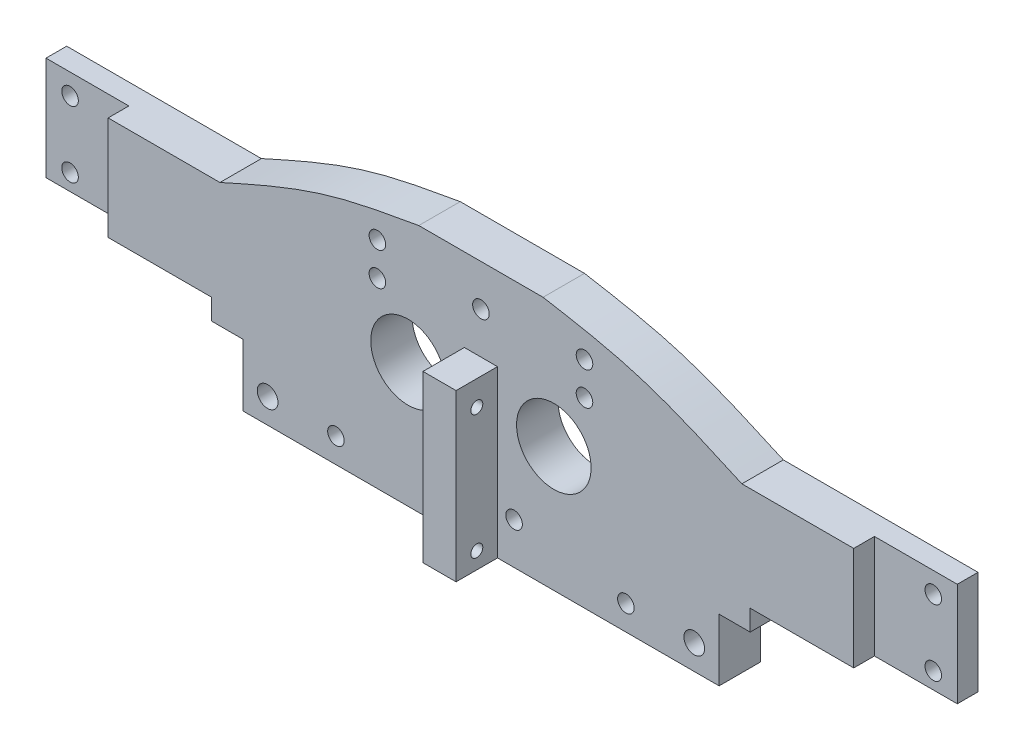
SolidWorks part; units mm, degrees
material "PLA Black"
ref_plane "Front Plane" through (0, 0, 0) normal (0, 0, 1) x (1, 0, 0)
ref_plane "Top Plane" through (0, 0, 0) normal (0, 1, 0) x (1, 0, 0)
ref_plane "Right Plane" through (0, 0, 0) normal (1, 0, 0) x (0, 0, -1)
sketch "Sketch1" plane through (0, 0, 0) normal (0, 0, 1) x (1, 0, 0)
  line L1 (-65, -22.5) -> (65, -22.5)
  line L2 (-65, -22.5) -> (-65, 7.5)
  line L3 (-65, 7.5) -> (-63, 7.5)
  line L4 (65, -22.5) -> (65, 7.5)
  line L5 (-15, 22.5) -> (15, 22.5)
  line L7 (63, 7.5) -> (65, 7.5)
  line L8 (0, 22.5) -> (0, -22.5) construction
  spline S0 degree 3 poles (15, 22.5) (22.4466, 21.1973) (39.0797, 18.2875) (54.4893, 11.3381) (63, 7.5) knots 0 0 0 0 0.4477 1 1 1 1
  spline S1 degree 3 poles (-15, 22.5) (-22.4466, 21.1973) (-39.0797, 18.2875) (-54.4893, 11.3381) (-63, 7.5) knots 0 0 0 0 0.4477 1 1 1 1
  point P10 (0, -22.5)
  point P11 (0, 0)
  dimension "D1" = 130
  dimension "D2" = 30
  dimension "D3" = 2
  dimension "D4" = 45
  dimension "D5" = 30
extrude "Extrude1" add sketch "Sketch1" along normal blind 10
sketch "Sketch2" plane through (0, 0, 0) normal (0, 0, 1) x (1, 0, 0)
  line L0 (-65, -22.5) -> (65, -22.5) construction
  line L1 (-57.5, -22.5) -> (57.5, -22.5)
  line L2 (-57.5, -22.5) -> (-57.5, -37.5)
  line L3 (-57.5, -37.5) -> (57.5, -37.5)
  line L4 (57.5, -22.5) -> (57.5, -37.5)
  point P6 (0, -37.5)
  dimension "D1" = 15
  dimension "D2" = 115
extrude "Extrude2" add sketch "Sketch2" along normal up to surface (10 mm away) up to face at (6, 3.75, 10)
hole_wizard "Ø4.0 (4) Diameter Hole1" positions "3DSketch1" profile "Sketch3" hole size "Ø4.0" standard "Ansi Metric"
sketch3d "3DSketch1"
  line L0 (57.5, -37.5, 10) -> (-57.5, -37.5, 10) construction
  line L5 (-35, -31.5, 10) -> (35, -31.5, 10) construction
  line L11 (0, -37.5, 10) -> (0, 22.5, 10) construction
  line L12 (15, 22.5, 10) -> (-15, 22.5, 10) construction
  point P0 (-35, -31.5, 10)
  point P2 (35, -31.5, 10)
  point P18 (0, -31.5, 10)
  dimension "D1" = 6
  dimension "D2" = 70
sketch "Sketch3" plane through (-35, -31.5, 10) normal (1, 0, 0) x (0, -1, 0)
  line L0 (0, 0) -> (0, 15)
  line L1 (0, 15) -> (2, 15)
  line L2 (2, 15) -> (2, 0)
  line L5 (2, 0) -> (0, 0)
  line L10 (0, 15) -> (-2, 15) construction
  line L11 (0, -6.35) -> (0, 107.95) construction
  dimension "Hole Dia." = 4
  dimension "Hole Depth" = 15
  dimension "Drill Angle" = 180
sketch "Sketch4" plane through (0, 0, 10) normal (0, 0, 1) x (1, 0, 0)
  line L0 (57.5, -37.5) -> (-57.5, -37.5) construction
  line L1 (4, 2.5) -> (-4, 2.5)
  line L2 (4, 2.5) -> (4, -37.5)
  line L3 (4, -37.5) -> (-4, -37.5)
  line L4 (-4, 2.5) -> (-4, -37.5)
  point P4 (0, 2.5)
  dimension "D1" = 40
  dimension "D2" = 8
extrude "Extrude3" add sketch "Sketch4" along normal blind 10
hole_wizard "Ø4.0 (4) Diameter Hole3" positions "3DSketch3" profile "Sketch7" hole size "Ø4.0" standard "Ansi Metric"
sketch3d "3DSketch3"
  line L0 (0, 22.5, 0) -> (0, -37.5, 0) construction
  line L1 (15, 22.5, 0) -> (-15, 22.5, 0) construction
  line L2 (-57.5, -37.5, 0) -> (57.5, -37.5, 0) construction
  point P0 (25, 14.5, 0)
  point P2 (-25, 14.5, 0)
  point P12 (25, 6.5, 0)
  point P14 (-25, 6.5, 0)
  dimension "D1" = 25
  dimension "D2" = 8
  dimension "D3" = 25
  dimension "D4" = 8
sketch "Sketch7" plane through (25, 14.5, 0) normal (1, 0, 0) x (0, 1, 0)
  line L0 (0, 0) -> (0, 15)
  line L1 (0, 15) -> (2, 15)
  line L2 (2, 15) -> (2, 0)
  line L5 (2, 0) -> (0, 0)
  line L10 (0, 15) -> (-2, 15) construction
  line L11 (0, -6.35) -> (0, 107.95) construction
  dimension "Hole Dia." = 4
  dimension "Hole Depth" = 15
  dimension "Drill Angle" = 180
hole_wizard "Ø5.0 (5) Diameter Hole1" positions "3DSketch4" profile "Sketch8" hole size "Ø5.0" standard "Ansi Metric"
sketch3d "3DSketch4"
  line L0 (35, -31.5, 0) -> (60.938, -31.5, 0) construction
  line L1 (35, -31.5, 0) -> (35, -31.5, 10) construction
  line L4 (57.5, -37.5, 0) -> (57.5, -22.5, 0) construction
  line L5 (0, -37.5, 0) -> (0, 22.5, 0) construction
  line L6 (-57.5, -37.5, 0) -> (57.5, -37.5, 0) construction
  line L7 (15, 22.5, 0) -> (-15, 22.5, 0) construction
  point P0 (51.5, -31.5, 0)
  dimension "D1" = 6
  dimension "D2" = 51.5
sketch "Sketch8" plane through (51.5, -31.5, 0) normal (1, 0, 0) x (0, 1, 0)
  line L0 (0, 0) -> (0, 15)
  line L1 (0, 15) -> (2.5, 15)
  line L2 (2.5, 15) -> (2.5, 0)
  line L5 (2.5, 0) -> (0, 0)
  line L10 (0, 15) -> (-2.5, 15) construction
  line L11 (0, -6.35) -> (0, 107.95) construction
  dimension "Hole Dia." = 5
  dimension "Hole Depth" = 15
  dimension "Drill Angle" = 180
hole_wizard "Ø4.0 (4) Diameter Hole5" positions "3DSketch5" profile "Sketch9" hole size "Ø4.0" standard "Ansi Metric"
sketch3d "3DSketch5"
  line L2 (0, 2.5, 10) -> (0, 12.5, 10) construction
  line L3 (4, 2.5, 10) -> (-4, 2.5, 10) construction
  line L6 (15, 22.5, 10) -> (-15, 22.5, 10) construction
  line L7 (57.5, -37.5, 10) -> (4, -37.5, 10) construction
  line L8 (0, 12.5, 10) -> (16.6362, 12.5, 10) construction
  point P0 (-8, -27.5, 10)
  point P2 (8, -27.5, 10)
  point P4 (0, 12.5, 10)
  dimension "D1" = 10
  dimension "D2" = 10
  dimension "D3" = 8
  dimension "D4" = 8
  dimension "D5" = 40
sketch "Sketch9" plane through (-8, -27.5, 10) normal (1, 0, 0) x (0, -1, 0)
  line L0 (0, 0) -> (0, 15)
  line L1 (0, 15) -> (2, 15)
  line L2 (2, 15) -> (2, 0)
  line L5 (2, 0) -> (0, 0)
  line L10 (0, 15) -> (-2, 15) construction
  line L11 (0, -6.35) -> (0, 107.95) construction
  dimension "Hole Dia." = 4
  dimension "Hole Depth" = 15
  dimension "Drill Angle" = 180
mirror "Mirror2" about plane through (0, 0, 0) normal (1, 0, 0) of "Ø5.0 (5) Diameter Hole1"
hole_wizard "Ø2.9 (2.9) Diameter Hole1" positions "3DSketch6" profile "Sketch10" hole size "Ø2.9" standard "Ansi Metric"
sketch3d "3DSketch6"
  line L0 (-4, 2.5, 15) -> (-4, -37.5, 15) construction
  line L1 (-4, 2.5, 20) -> (-4, 2.5, 10) construction
  line L2 (-4, -37.5, 20) -> (-4, -37.5, 10) construction
  point P0 (-4, -3.5, 15)
  point P2 (-4, -33.5, 15)
  dimension "D1" = 30
  dimension "D2" = 4
sketch "Sketch10" plane through (-4, -3.5, 15) normal (0, 1, 0) x (0, 0, 1)
  line L0 (0, 0) -> (0, 10)
  line L1 (0, 10) -> (1.45, 10)
  line L2 (1.45, 10) -> (1.45, 0)
  line L5 (1.45, 0) -> (0, 0)
  line L10 (0, 10) -> (-1.45, 10) construction
  line L11 (0, -6.35) -> (0, 107.95) construction
  dimension "Hole Dia." = 2.9
  dimension "Hole Depth" = 10
  dimension "Drill Angle" = 180
sketch "Sketch11" plane through (0, 0, 10) normal (0, 0, 1) x (1, 0, 0)
  circle A0 centre (-17.5978, -7.3692) radius 9
  dimension "D1" = 18
extrude "Extrude5" cut sketch "Sketch11" against normal blind 10
mirror "Mirror3" about plane through (0, 0, 0) normal (1, 0, 0) of "Extrude5"
sketch "Sketch12" plane through (0, 0, 0) normal (0, 0, 1) x (1, 0, 0)
  line L1 (-65, 7.5) -> (-110, 7.5)
  line L2 (-65, 7.5) -> (-65, -17.5)
  line L3 (-65, -17.5) -> (-110, -17.5)
  line L4 (-110, 7.5) -> (-110, -17.5)
  dimension "D1" = 45
  dimension "D2" = 25
extrude "Extrude6" add sketch "Sketch12" along normal up to surface (10 mm away) up to face at (5.875, -10, 10)
sketch "Sketch14" plane through (0, 0, 10) normal (0, 0, 1) x (1, 0, 0)
  line L0 (-65, -17.5) -> (-110, -17.5) construction
  line L1 (-110, 7.5) -> (-90, 7.5)
  line L2 (-110, 7.5) -> (-110, -17.5)
  line L3 (-110, -17.5) -> (-90, -17.5)
  line L4 (-90, 7.5) -> (-90, -17.5)
  dimension "D1" = 20
extrude "Extrude8" cut sketch "Sketch14" against normal blind 5
hole_wizard "Ø4.0 (4) Diameter Hole6" positions "3DSketch7" profile "Sketch15" hole size "Ø4.0" standard "Ansi Metric"
sketch3d "3DSketch7"
  line L0 (-110, 7.5, 5) -> (-110, -17.5, 5) construction
  line L1 (-90, 7.5, 5) -> (-110, 7.5, 5) construction
  point P0 (-104.2, 2.5, 5)
  point P2 (-104.2, -13.5, 5)
  dimension "D1" = 16
  dimension "D2" = 5.8
  dimension "D3" = 5
sketch "Sketch15" plane through (-104.2, 2.5, 5) normal (1, 0, 0) x (0, -1, 0)
  line L0 (0, 0) -> (0, 15)
  line L1 (0, 15) -> (2, 15)
  line L2 (2, 15) -> (2, 0)
  line L5 (2, 0) -> (0, 0)
  line L10 (0, 15) -> (-2, 15) construction
  line L11 (0, -6.35) -> (0, 107.95) construction
  dimension "Hole Dia." = 4
  dimension "Hole Depth" = 15
  dimension "Drill Angle" = 180
mirror "Mirror5" about plane through (0, 0, 0) normal (1, 0, 0) of "Ø4.0 (4) Diameter Hole6", "Extrude8", "Extrude6"
